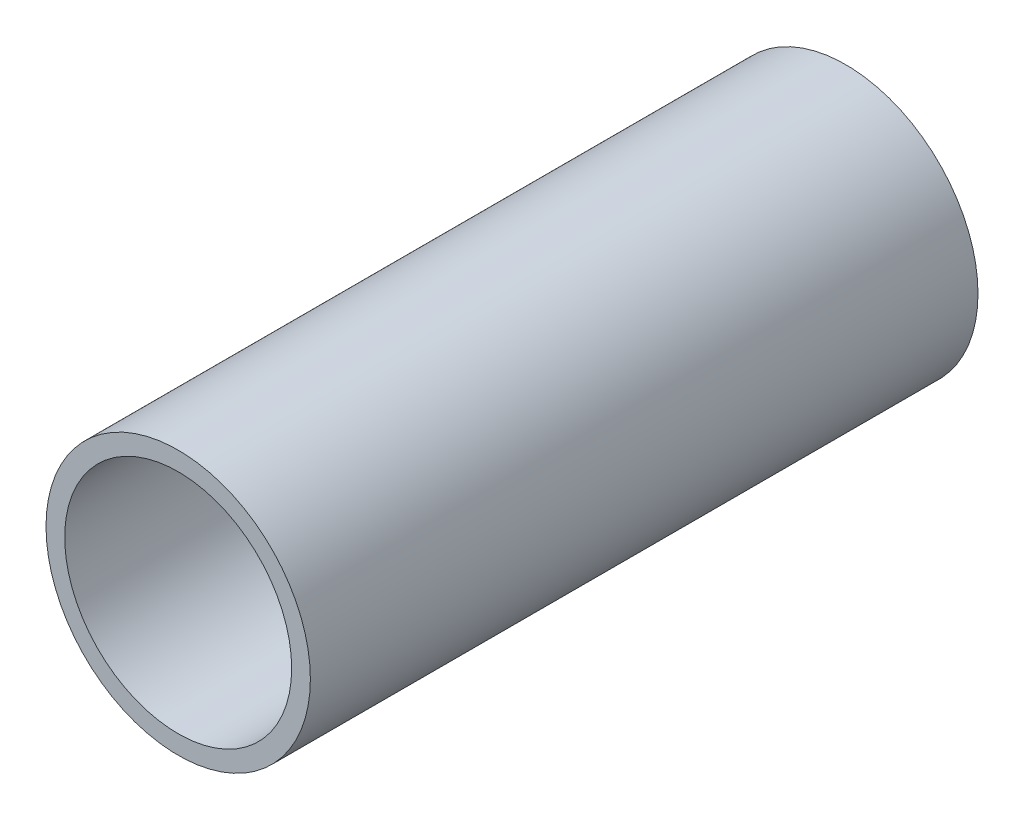
SolidWorks part; units mm, degrees
material "PVC Rigid"
ref_plane "Front Plane" through (0, 0, 0) normal (0, 0, 1) x (1, 0, 0)
ref_plane "Top Plane" through (0, 0, 0) normal (0, 1, 0) x (1, 0, 0)
ref_plane "Right Plane" through (0, 0, 0) normal (1, 0, 0) x (0, 0, -1)
sketch "Sketch1" plane through (0, 0, 0) normal (0, 0, 1) x (1, 0, 0)
  circle A1 centre (0, 0) radius 12.573
  circle A2 centre (0, 0) radius 10.795
  dimension "D1" = 25.146
  dimension "D2" = 21.59
extrude "Boss-Extrude1" add sketch "Sketch1" along normal blind 63.5
